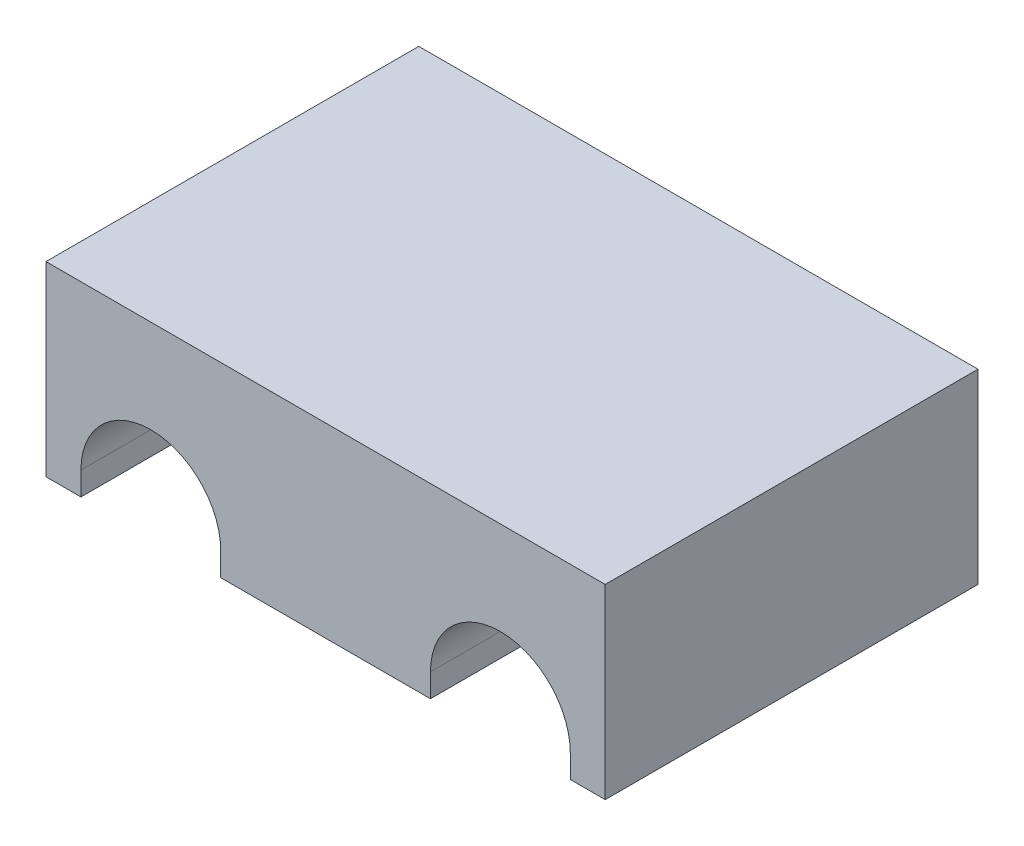
SolidWorks part; units mm, degrees
ref_plane "Alzado" through (0, 0, 0) normal (0, 0, 1) x (1, 0, 0)
ref_plane "Planta" through (0, 0, 0) normal (0, 1, 0) x (1, 0, 0)
ref_plane "Vista lateral" through (0, 0, 0) normal (1, 0, 0) x (0, 0, -1)
sketch "Croquis2" plane through (0, 0, 0) normal (0, 0, 1) x (1, 0, 0)
  line L0 (39.6925, 0) -> (39.6925, 25.4) construction
  line L2 (15.88, 0) -> (63.505, 0) construction
  line L3 (1.5925, -25.4) -> (77.7925, -25.4)
  line L4 (1.5925, -25.4) -> (1.5925, 25.4)
  line L5 (1.5925, 25.4) -> (77.7925, 25.4)
  line L6 (77.7925, -25.4) -> (77.7925, 25.4)
  line L7 (1.5925, -25.4) -> (77.7925, 25.4) construction
  line L8 (1.5925, 25.4) -> (77.7925, -25.4) construction
  circle A0 centre (15.88, 0) radius 9.525
  circle A1 centre (63.505, 0) radius 9.525
  dimension "D2" = 19.05
  dimension "D3" = 47.625
  dimension "D4" = 19.05
  dimension "D1" = 25.4
  dimension "D5" = 76.2
extrude "Saliente-Extruir1" add sketch "Croquis2" along normal blind 50.8
sketch "Croquis3" plane through (0, 0, 50.8) normal (0, 0, 1) x (1, 0, 0)
  line L0 (1.5925, 0) -> (77.7925, 0)
  line L1 (1.5925, 25.4) -> (1.5925, -25.4) construction
  line L2 (77.7925, -25.4) -> (77.7925, 25.4) construction
  line L3 (1.5925, 0) -> (1.5925, -25.4)
  line L4 (1.5925, -25.4) -> (77.7925, -25.4)
  line L5 (77.7925, -25.4) -> (77.7925, 0)
extrude "Cortar-Extruir1" cut sketch "Croquis3" against normal blind 50.8
sketch "Croquis4" plane through (0, 0, 50.8) normal (0, 0, 1) x (1, 0, 0)
  line L0 (39.6925, 0) -> (39.6925, 16.4361) construction
  line L1 (15.88, 9.525) -> (15.88, 12.7) construction
  line L2 (15.88, 9.525) -> (15.88, 3.175) construction
  line L3 (53.98, 0) -> (25.405, 0) construction
  line L5 (63.505, 9.525) -> (63.505, 3.175) construction
  line L6 (63.505, 9.525) -> (63.505, 12.7) construction
  line L7 (6.355, 0) -> (6.355, 3.175)
  line L8 (25.405, 0) -> (25.405, 3.175)
  line L9 (6.355, 0) -> (25.405, 0)
  line L10 (73.03, 0) -> (53.98, 0)
  line L11 (53.98, 0) -> (53.98, 3.175)
  line L12 (73.03, 0) -> (73.03, 3.175)
  arc A1 (25.405, 0) -> (6.355, 0) centre (15.88, 0) ccw construction
  arc A2 (25.405, 3.175) -> (6.355, 3.175) centre (15.88, 3.175) ccw
  arc A3 (53.98, 3.175) -> (73.03, 3.175) centre (63.505, 3.175) cw
  dimension "D2" = 3.175
  dimension "D3" = 9.525
extrude "Cortar-Extruir2" cut sketch "Croquis4" against normal blind 50.8
